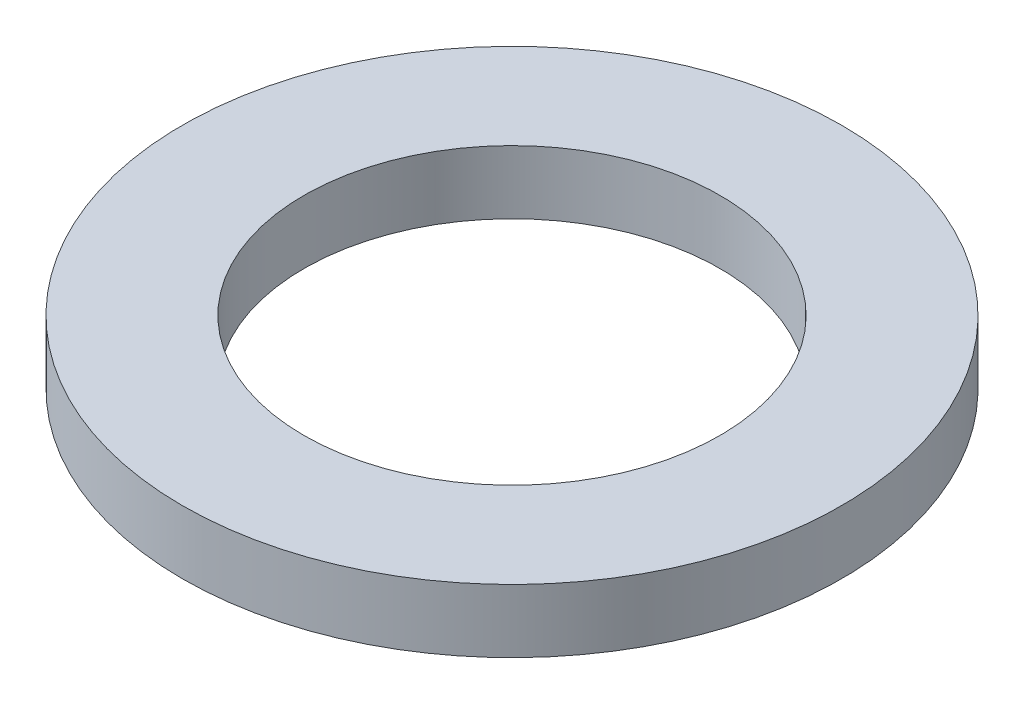
SolidWorks part; units mm, degrees
material "Balsa"
ref_plane "Front Plane" through (0, 0, 0) normal (0, 0, 1) x (1, 0, 0)
ref_plane "Top Plane" through (0, 0, 0) normal (0, 1, 0) x (1, 0, 0)
ref_plane "Right Plane" through (0, 0, 0) normal (1, 0, 0) x (0, 0, -1)
sketch "Sketch1" plane through (0, 0, 0) normal (0, 1, 0) x (1, 0, 0)
  circle A0 centre (0, 0) radius 66.04
  circle A1 centre (0, 0) radius 41.6814
  dimension "D1" = 132.08
  dimension "D2" = 83.3628
extrude "Boss-Extrude1" add sketch "Sketch1" along normal blind 12.7
